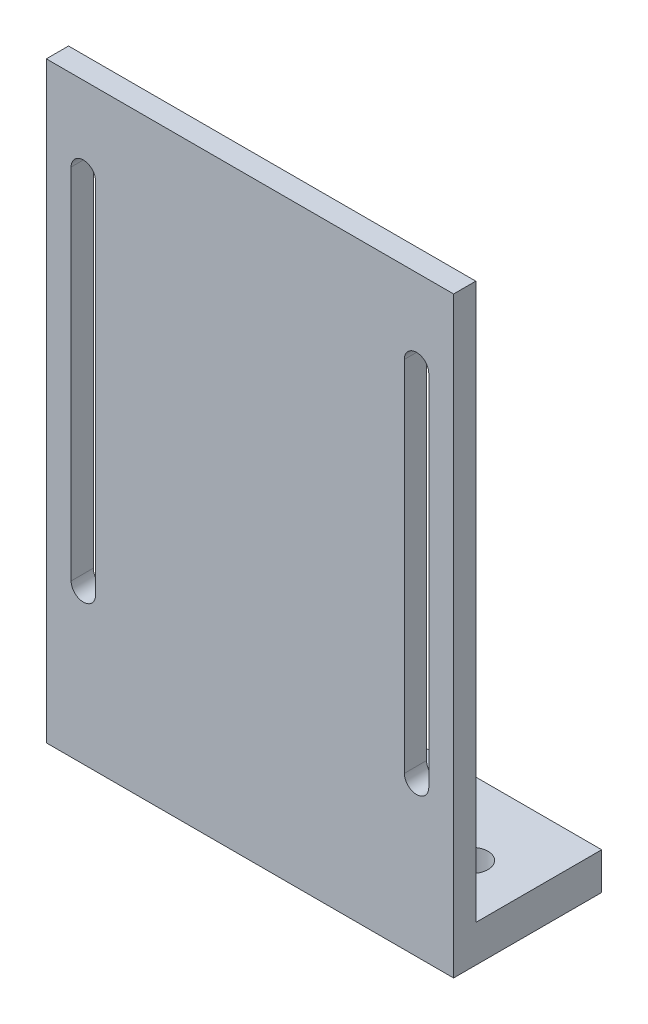
SolidWorks part; units mm, degrees
ref_plane "Front Plane" through (0, 0, 0) normal (0, 0, 1) x (1, 0, 0)
ref_plane "Top Plane" through (0, 0, 0) normal (0, 1, 0) x (1, 0, 0)
ref_plane "Right Plane" through (0, 0, 0) normal (1, 0, 0) x (0, 0, -1)
sketch "Sketch1" plane through (0, 0, 0) normal (0, 1, 0) x (1, 0, 0)
  line L0 (-27.5, 0) -> (27.5, 0) construction
  line L1 (-27.5, 10) -> (27.5, 10)
  line L2 (-27.5, 10) -> (-27.5, -10)
  line L3 (-27.5, -10) -> (27.5, -10)
  line L4 (27.5, 10) -> (27.5, -10)
  line L5 (-27.5, 10) -> (27.5, -10) construction
  line L6 (-27.5, -10) -> (27.5, 10) construction
  circle A0 centre (-20, 0) radius 2.15
  circle A1 centre (20, 0) radius 2.15
  point P0 (0, 0)
  point P14 (0, 0)
  dimension "D3" = 4.3
  dimension "D4" = 4.3
  dimension "D1" = 20
  dimension "D2" = 55
  dimension "D5" = 20
  dimension "D6" = 40
extrude "Boss-Extrude1" add sketch "Sketch1" along normal blind 5
sketch "Sketch2" plane through (0, 5, 0) normal (0, 1, 0) x (1, 0, 0)
  line L1 (-27.5, 10) -> (-27.5, -10) construction
  line L2 (-27.5, -7) -> (27.5, -7)
  line L3 (-27.5, -7) -> (-27.5, -10)
  line L4 (-27.5, -10) -> (27.5, -10)
  line L5 (27.5, -7) -> (27.5, -10)
  dimension "D1" = 3
extrude "Boss-Extrude2" add sketch "Sketch2" along normal blind 75
sketch "Sketch3" plane through (0, 0, 7) normal (0, 0, -1) x (-1, 0, 0)
  line L0 (-22.5, 69.0223) -> (-22.5, 20.6089) construction
  line L1 (-20.85, 69.0223) -> (-20.85, 20.6089)
  line L2 (-24.15, 69.0223) -> (-24.15, 20.6089)
  line L3 (0, 5) -> (0, 80) construction
  line L4 (-27.5, 5) -> (27.5, 5) construction
  line L5 (-27.5, 80) -> (27.5, 80) construction
  line L6 (22.5, 69.0223) -> (22.5, 20.6089) construction
  line L7 (20.85, 69.0223) -> (20.85, 20.6089)
  line L8 (24.15, 69.0223) -> (24.15, 20.6089)
  arc A0 (-20.85, 69.0223) -> (-24.15, 69.0223) centre (-22.5, 69.0223) ccw
  arc A1 (-24.15, 20.6089) -> (-20.85, 20.6089) centre (-22.5, 20.6089) ccw
  arc A2 (20.85, 69.0223) -> (24.15, 69.0223) centre (22.5, 69.0223) cw
  arc A3 (24.15, 20.6089) -> (20.85, 20.6089) centre (22.5, 20.6089) cw
  point P2 (-22.5, 44.8156)
  point P15 (22.5, 44.8156)
  dimension "D1" = 3.3
  dimension "D2" = 22.5
extrude "Cut-Extrude1" cut sketch "Sketch3" against normal blind 75
